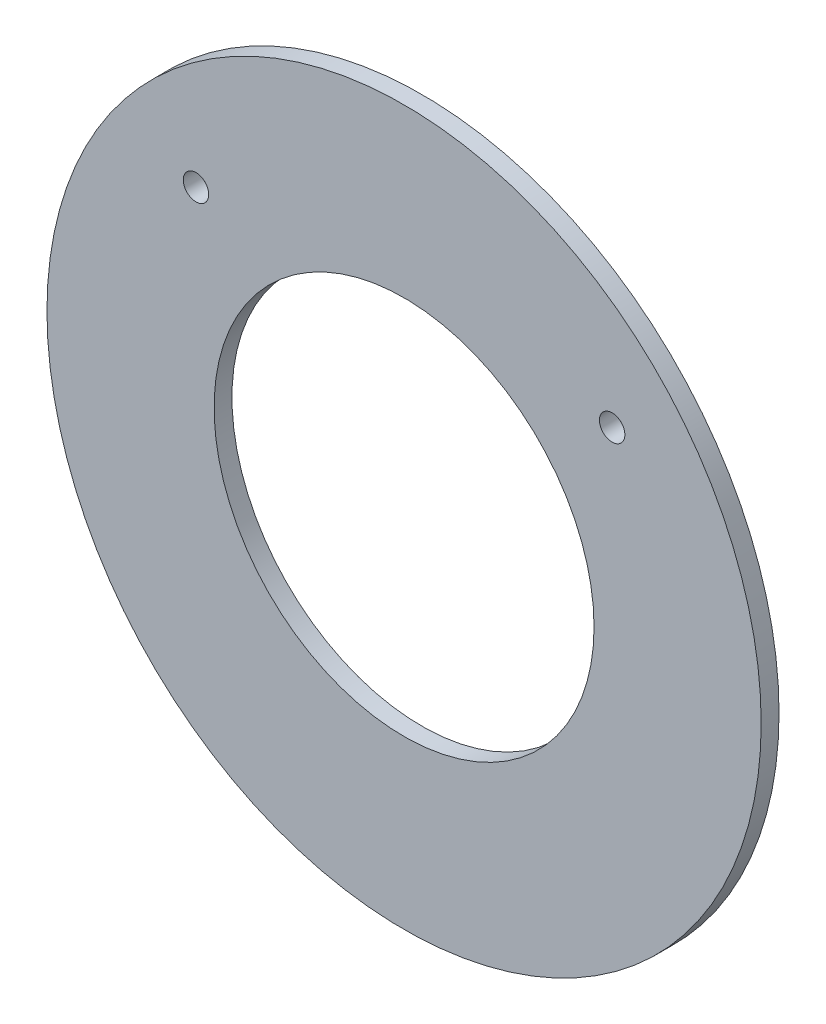
SolidWorks part; units mm, degrees
ref_plane "Front Plane" through (0, 0, 0) normal (0, 0, 1) x (1, 0, 0)
ref_plane "Top Plane" through (0, 0, 0) normal (0, 1, 0) x (1, 0, 0)
ref_plane "Right Plane" through (0, 0, 0) normal (1, 0, 0) x (0, 0, -1)
sketch "Sketch1" plane through (0, 0, 0) normal (0, 0, 1) x (1, 0, 0)
  line L0 (25.5, 38.31) -> (25.5, 0) construction
  line L1 (0, 38.31) -> (51, 38.31) construction
  line L2 (0, 38.31) -> (0, 0) construction
  line L3 (0, 0) -> (51, 0) construction
  line L4 (51, 38.31) -> (51, 0) construction
  circle A0 centre (25.5, 19.155) radius 16.891
  circle A1 centre (25.5, 19.155) radius 31.75
  dimension "D3" = 33.782
  dimension "D4" = 63.5
  dimension "D1" = 38.31
  dimension "D2" = 51
extrude "Boss-Extrude1" add sketch "Sketch1" along normal blind 1.5875
sketch "Sketch2" plane through (0, 0, 0) normal (0, 0, -1) x (-1, 0, 0)
  line L0 (-44, 35.31) -> (-7, 35.31) construction
  line L1 (-25.5, 38.31) -> (-25.5, 35.31) construction
  line L2 (0, 38.31) -> (-51, 38.31) construction
  circle A0 centre (-7, 35.31) radius 1.1303
  circle A1 centre (-44, 35.31) radius 1.1303
  point P10 (-46.3647, 6.5886)
  dimension "D2" = 2.2606
  dimension "D3" = 3
  dimension "D1" = 37
extrude "Cut-Extrude1" cut sketch "Sketch2" against normal up to surface (1.5875 mm away) up to face at (57.25, 19.155, 1.5875)
